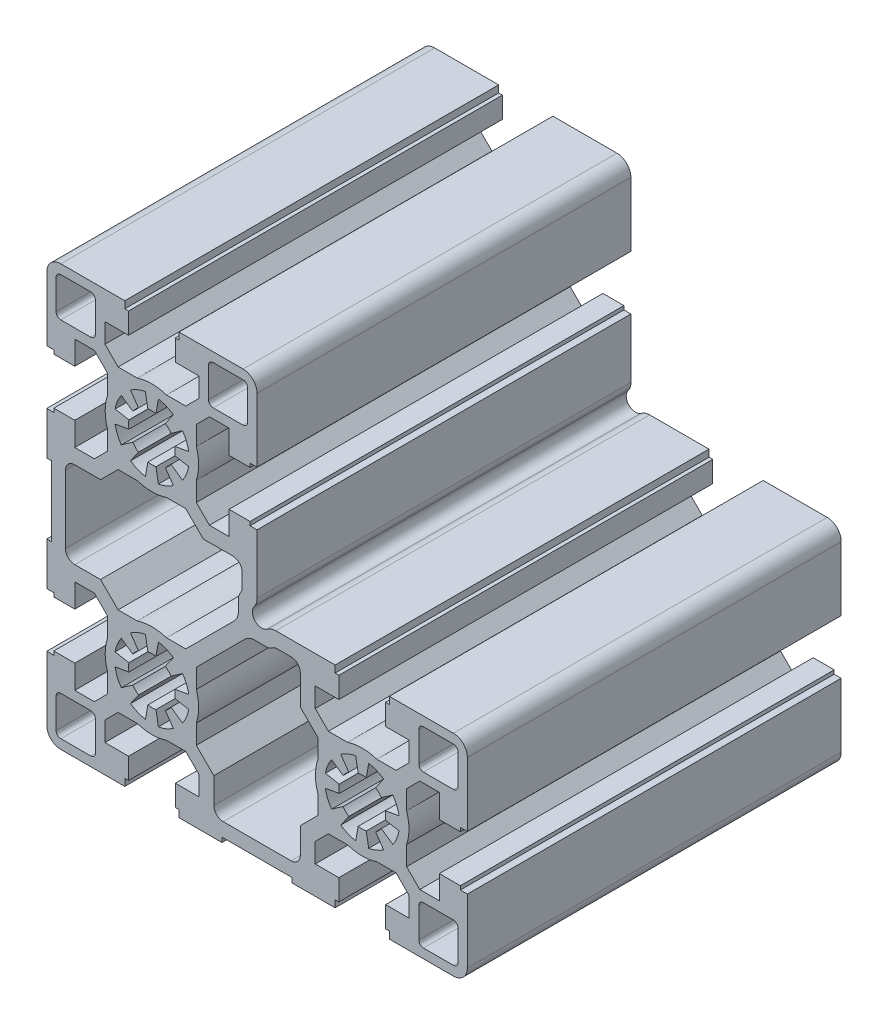
SolidWorks part; units mm, degrees
ref_plane "Front Plane" through (0, 0, 0) normal (0, 0, 1) x (1, 0, 0)
ref_plane "Top Plane" through (0, 0, 0) normal (0, 1, 0) x (1, 0, 0)
ref_plane "Right Plane" through (0, 0, 0) normal (1, 0, 0) x (0, 0, -1)
sketch "Sketch1" plane through (0, 0, 0) normal (0, 0, 1) x (1, 0, 0)
  line L0 (3.1734, -19.3822) -> (3.1734, -25.7822)
  line L1 (2.1734, -26.7822) -> (-4.2266, -26.7822)
  line L2 (-5.2266, -25.7822) -> (-5.2266, -19.3822)
  line L3 (-4.2266, -18.3822) -> (2.1734, -18.3822)
  line L4 (-81.8266, 61.2178) -> (-68.1266, 61.2178)
  line L5 (-56.5266, 61.2178) -> (-42.8266, 61.2178)
  line L6 (-36.9207, 12.4814) -> (-36.443, 12.7543)
  line L7 (-35.4507, 13.0178) -> (-32.5771, 13.0178)
  line L8 (-30.5771, 11.0178) -> (-30.5771, 4.7055)
  line L9 (-30.5771, 4.7055) -> (-26.8266, 0.9551)
  line L10 (-26.8266, 0.9551) -> (-26.8266, -3.1597)
  line L11 (-26.8266, -9.4047) -> (-26.8266, -13.5194)
  line L12 (-26.8266, -13.5194) -> (-30.5771, -17.2698)
  line L13 (-30.5771, -17.2698) -> (-30.5771, -22.7822)
  line L14 (-32.5771, -24.7822) -> (-47.0766, -24.7822)
  line L15 (-49.0766, -22.7822) -> (-49.0766, -17.2694)
  line L16 (-49.0766, -17.2694) -> (-52.8266, -13.5194)
  line L17 (-52.8266, -13.5194) -> (-52.8266, -9.4047)
  line L18 (-52.8266, -3.1597) -> (-52.8266, 0.9551)
  line L19 (-52.8266, 0.9551) -> (-42.4426, 11.3392)
  line L20 (-40.3212, 12.2178) -> (-37.9129, 12.2178)
  line L21 (-18.7158, 1.5963) -> (-18.1949, -1.3581)
  line L22 (-16.4584, -1.3581) -> (-15.9374, 1.5963)
  line L23 (-12.738, 0.2711) -> (-14.4587, -2.1864)
  line L24 (-13.2309, -3.4143) -> (-10.7734, -1.6935)
  line L25 (-9.4482, -4.893) -> (-12.4026, -5.4139)
  line L26 (-12.4026, -7.1504) -> (-9.4482, -7.6713)
  line L27 (-10.7734, -10.8708) -> (-13.2309, -9.15)
  line L28 (-14.4587, -10.3779) -> (-12.738, -12.8354)
  line L29 (-15.9374, -14.1606) -> (-16.4584, -11.2062)
  line L30 (-18.1949, -11.2062) -> (-18.7158, -14.1606)
  line L31 (-21.9152, -12.8354) -> (-20.1945, -10.3779)
  line L32 (-21.4224, -9.15) -> (-23.8798, -10.8708)
  line L33 (-25.2051, -7.6713) -> (-22.2507, -7.1504)
  line L34 (-22.2507, -5.4139) -> (-25.2051, -4.893)
  line L35 (-23.8798, -1.6935) -> (-21.4224, -3.4143)
  line L36 (-20.1945, -2.1864) -> (-21.9152, 0.2711)
  line L37 (-39.8266, 32.9178) -> (-39.8266, 20.2211)
  line L38 (-41.3266, 32.9178) -> (-39.8266, 32.9178)
  line L39 (-41.3266, 33.7178) -> (-41.3266, 32.9178)
  line L40 (-45.8266, 33.7178) -> (-41.3266, 33.7178)
  line L41 (-45.8266, 28.6678) -> (-45.8266, 33.7178)
  line L42 (-50.0139, 28.6678) -> (-45.8266, 28.6678)
  line L43 (-52.8266, 31.4806) -> (-50.0139, 28.6678)
  line L44 (-52.8266, 35.5953) -> (-52.8266, 31.4806)
  line L45 (-52.8266, 45.9551) -> (-52.8266, 41.8403)
  line L46 (-50.0139, 48.7678) -> (-52.8266, 45.9551)
  line L47 (-45.8266, 48.7678) -> (-50.0139, 48.7678)
  line L48 (-45.8266, 43.7178) -> (-45.8266, 48.7678)
  line L49 (-41.3266, 43.7178) -> (-45.8266, 43.7178)
  line L50 (-41.3266, 44.5178) -> (-41.3266, 43.7178)
  line L51 (-39.8266, 44.5178) -> (-41.3266, 44.5178)
  line L52 (-39.8266, 58.2178) -> (-39.8266, 44.5178)
  line L53 (-57.3266, 59.7178) -> (-56.5266, 59.7178)
  line L54 (-57.3266, 55.2178) -> (-57.3266, 59.7178)
  line L55 (-52.2766, 55.2178) -> (-57.3266, 55.2178)
  line L56 (-52.2766, 51.0306) -> (-52.2766, 55.2178)
  line L57 (-55.0894, 48.2178) -> (-52.2766, 51.0306)
  line L58 (-59.2041, 48.2178) -> (-55.0894, 48.2178)
  line L59 (-69.5639, 48.2178) -> (-65.4491, 48.2178)
  line L60 (-72.3766, 51.0306) -> (-69.5639, 48.2178)
  line L61 (-72.3766, 55.2178) -> (-72.3766, 51.0306)
  line L62 (-67.3266, 55.2178) -> (-72.3766, 55.2178)
  line L63 (-67.3266, 59.7178) -> (-67.3266, 55.2178)
  line L64 (-68.1266, 59.7178) -> (-67.3266, 59.7178)
  line L65 (-84.8266, 44.5178) -> (-84.8266, 58.2178)
  line L66 (-83.3266, 44.5178) -> (-84.8266, 44.5178)
  line L67 (-83.3266, 43.7178) -> (-83.3266, 44.5178)
  line L68 (-78.8266, 43.7178) -> (-83.3266, 43.7178)
  line L69 (-78.8266, 48.7678) -> (-78.8266, 43.7178)
  line L70 (-74.6394, 48.7678) -> (-78.8266, 48.7678)
  line L71 (-71.8266, 45.9551) -> (-74.6394, 48.7678)
  line L72 (-71.8266, 41.8403) -> (-71.8266, 45.9551)
  line L73 (-71.8266, 31.4806) -> (-71.8266, 35.5953)
  line L74 (-74.6394, 28.6678) -> (-71.8266, 31.4806)
  line L75 (-78.8266, 28.6678) -> (-74.6394, 28.6678)
  line L76 (-78.8266, 33.7178) -> (-78.8266, 28.6678)
  line L77 (-83.3266, 33.7178) -> (-78.8266, 33.7178)
  line L78 (-83.3266, 32.9178) -> (-83.3266, 33.7178)
  line L79 (-84.8266, 32.9178) -> (-83.3266, 32.9178)
  line L80 (-84.8266, 23.7178) -> (-84.8266, 32.9178)
  line L81 (-83.8266, 23.7178) -> (-84.8266, 23.7178)
  line L82 (-83.8266, 8.7178) -> (-83.8266, 23.7178)
  line L83 (-84.8266, 8.7178) -> (-83.8266, 8.7178)
  line L84 (-84.8266, -0.4822) -> (-84.8266, 8.7178)
  line L85 (-83.3266, -0.4822) -> (-84.8266, -0.4822)
  line L86 (-83.3266, -1.2822) -> (-83.3266, -0.4822)
  line L87 (-78.8266, -1.2822) -> (-83.3266, -1.2822)
  line L88 (-78.8266, 3.7678) -> (-78.8266, -1.2822)
  line L89 (-74.6394, 3.7678) -> (-78.8266, 3.7678)
  line L90 (-71.8266, 0.9551) -> (-74.6394, 3.7678)
  line L91 (-71.8266, -3.1597) -> (-71.8266, 0.9551)
  line L92 (-71.8266, -13.5194) -> (-71.8266, -9.4047)
  line L93 (-74.6394, -16.3322) -> (-71.8266, -13.5194)
  line L94 (-78.8266, -16.3322) -> (-74.6394, -16.3322)
  line L95 (-78.8266, -11.2822) -> (-78.8266, -16.3322)
  line L96 (-83.3266, -11.2822) -> (-78.8266, -11.2822)
  line L97 (-83.3266, -12.0822) -> (-83.3266, -11.2822)
  line L98 (-84.8266, -12.0822) -> (-83.3266, -12.0822)
  line L99 (-84.8266, -25.7822) -> (-84.8266, -12.0822)
  line L100 (-68.1266, -28.7822) -> (-81.8266, -28.7822)
  line L101 (-68.1266, -27.2822) -> (-68.1266, -28.7822)
  line L102 (-67.3266, -27.2822) -> (-68.1266, -27.2822)
  line L103 (-67.3266, -22.7822) -> (-67.3266, -27.2822)
  line L104 (-72.3766, -22.7822) -> (-67.3266, -22.7822)
  line L105 (-72.3766, -18.5949) -> (-72.3766, -22.7822)
  line L106 (-69.5639, -15.7822) -> (-72.3766, -18.5949)
  line L107 (-65.4491, -15.7822) -> (-69.5639, -15.7822)
  line L108 (-55.0894, -15.7822) -> (-59.2041, -15.7822)
  line L109 (-52.2766, -18.5949) -> (-55.0894, -15.7822)
  line L110 (-52.2766, -22.7822) -> (-52.2766, -18.5949)
  line L111 (-57.3266, -22.7822) -> (-52.2766, -22.7822)
  line L112 (-57.3266, -27.2822) -> (-57.3266, -22.7822)
  line L113 (-56.5266, -27.2822) -> (-57.3266, -27.2822)
  line L114 (-56.5266, -28.7822) -> (-56.5266, -27.2822)
  line L115 (-47.3266, -28.7822) -> (-56.5266, -28.7822)
  line L116 (-47.3266, -27.7822) -> (-47.3266, -28.7822)
  line L117 (-32.3266, -27.7822) -> (-47.3266, -27.7822)
  line L118 (-32.3266, -28.7822) -> (-32.3266, -27.7822)
  line L119 (-23.1266, -28.7822) -> (-32.3266, -28.7822)
  line L120 (-23.1266, -27.2822) -> (-23.1266, -28.7822)
  line L121 (-22.3266, -27.2822) -> (-23.1266, -27.2822)
  line L122 (-22.3266, -22.7822) -> (-22.3266, -27.2822)
  line L123 (-27.3766, -22.7822) -> (-22.3266, -22.7822)
  line L124 (-27.3766, -18.5949) -> (-27.3766, -22.7822)
  line L125 (-24.5639, -15.7822) -> (-27.3766, -18.5949)
  line L126 (-20.4491, -15.7822) -> (-24.5639, -15.7822)
  line L127 (-10.0894, -15.7822) -> (-14.2041, -15.7822)
  line L128 (-7.2766, -18.5949) -> (-10.0894, -15.7822)
  line L129 (-7.2766, -22.7822) -> (-7.2766, -18.5949)
  line L130 (-12.3266, -22.7822) -> (-7.2766, -22.7822)
  line L131 (-12.3266, -27.2822) -> (-12.3266, -22.7822)
  line L132 (-11.5266, -27.2822) -> (-12.3266, -27.2822)
  line L133 (-11.5266, -28.7822) -> (-11.5266, -27.2822)
  line L134 (2.1734, -28.7822) -> (-11.5266, -28.7822)
  line L135 (5.1734, -12.0822) -> (5.1734, -25.7822)
  line L136 (3.6734, -12.0822) -> (5.1734, -12.0822)
  line L137 (3.6734, -11.2822) -> (3.6734, -12.0822)
  line L138 (-0.8266, -11.2822) -> (3.6734, -11.2822)
  line L139 (-0.8266, -16.3322) -> (-0.8266, -11.2822)
  line L140 (-5.0139, -16.3322) -> (-0.8266, -16.3322)
  line L141 (-7.8266, -13.5194) -> (-5.0139, -16.3322)
  line L142 (-7.8266, -9.4047) -> (-7.8266, -13.5194)
  line L143 (-7.8266, 0.9551) -> (-7.8266, -3.1597)
  line L144 (-5.0139, 3.7678) -> (-7.8266, 0.9551)
  line L145 (-0.8266, 3.7678) -> (-5.0139, 3.7678)
  line L146 (-0.8266, -1.2822) -> (-0.8266, 3.7678)
  line L147 (3.6734, -1.2822) -> (-0.8266, -1.2822)
  line L148 (3.6734, -0.4822) -> (3.6734, -1.2822)
  line L149 (5.1734, -0.4822) -> (3.6734, -0.4822)
  line L150 (5.1734, 13.2178) -> (5.1734, -0.4822)
  line L151 (-11.5266, 16.2178) -> (2.1734, 16.2178)
  line L152 (-11.5266, 14.7178) -> (-11.5266, 16.2178)
  line L153 (-12.3266, 14.7178) -> (-11.5266, 14.7178)
  line L154 (-12.3266, 10.2178) -> (-12.3266, 14.7178)
  line L155 (-7.2766, 10.2178) -> (-12.3266, 10.2178)
  line L156 (-7.2766, 6.0306) -> (-7.2766, 10.2178)
  line L157 (-10.0894, 3.2178) -> (-7.2766, 6.0306)
  line L158 (-14.2041, 3.2178) -> (-10.0894, 3.2178)
  line L159 (-24.5639, 3.2178) -> (-20.4491, 3.2178)
  line L160 (-27.3766, 6.0306) -> (-24.5639, 3.2178)
  line L161 (-27.3766, 10.2178) -> (-27.3766, 6.0306)
  line L162 (-22.3266, 10.2178) -> (-27.3766, 10.2178)
  line L163 (-22.3266, 14.7178) -> (-22.3266, 10.2178)
  line L164 (-23.1266, 14.7178) -> (-22.3266, 14.7178)
  line L165 (-23.1266, 16.2178) -> (-23.1266, 14.7178)
  line L166 (-35.8233, 16.2178) -> (-23.1266, 16.2178)
  line L167 (-4.2266, 14.2178) -> (2.1734, 14.2178)
  line L168 (3.1734, 13.2178) -> (3.1734, 6.8178)
  line L169 (2.1734, 5.8178) -> (-4.2266, 5.8178)
  line L170 (-5.2266, 6.8178) -> (-5.2266, 13.2178)
  line L171 (-42.8266, 50.8178) -> (-49.2266, 50.8178)
  line L172 (-50.2266, 51.8178) -> (-50.2266, 58.2178)
  line L173 (-49.2266, 59.2178) -> (-42.8266, 59.2178)
  line L174 (-41.8266, 58.2178) -> (-41.8266, 51.8178)
  line L175 (-63.7158, 46.5963) -> (-63.1949, 43.6419)
  line L176 (-61.4584, 43.6419) -> (-60.9374, 46.5963)
  line L177 (-57.738, 45.2711) -> (-59.4587, 42.8136)
  line L178 (-58.2309, 41.5857) -> (-55.7734, 43.3065)
  line L179 (-54.4482, 40.107) -> (-57.4026, 39.5861)
  line L180 (-57.4026, 37.8496) -> (-54.4482, 37.3287)
  line L181 (-55.7734, 34.1292) -> (-58.2309, 35.85)
  line L182 (-59.4587, 34.6221) -> (-57.738, 32.1646)
  line L183 (-60.9374, 30.8394) -> (-61.4584, 33.7938)
  line L184 (-63.1949, 33.7938) -> (-63.7158, 30.8394)
  line L185 (-66.9152, 32.1646) -> (-65.1945, 34.6221)
  line L186 (-66.4224, 35.85) -> (-68.8798, 34.1292)
  line L187 (-70.2051, 37.3287) -> (-67.2507, 37.8496)
  line L188 (-67.2507, 39.5861) -> (-70.2051, 40.107)
  line L189 (-68.8798, 43.3065) -> (-66.4224, 41.5857)
  line L190 (-65.1945, 42.8136) -> (-66.9152, 45.2711)
  line L191 (-44.7053, 13.6019) -> (-55.0894, 3.2178)
  line L192 (-55.0894, 3.2178) -> (-59.2041, 3.2178)
  line L193 (-65.4491, 3.2178) -> (-69.5639, 3.2178)
  line L194 (-69.5639, 3.2178) -> (-73.3139, 6.9678)
  line L195 (-73.3139, 6.9678) -> (-78.8266, 6.9678)
  line L196 (-80.8266, 8.9678) -> (-80.8266, 23.4674)
  line L197 (-78.8266, 25.4674) -> (-73.3143, 25.4674)
  line L198 (-73.3143, 25.4674) -> (-69.5639, 29.2178)
  line L199 (-69.5639, 29.2178) -> (-65.4491, 29.2178)
  line L200 (-59.2041, 29.2178) -> (-55.0894, 29.2178)
  line L201 (-55.0894, 29.2178) -> (-51.3389, 25.4674)
  line L202 (-51.3389, 25.4674) -> (-45.0266, 25.4674)
  line L203 (-43.0266, 23.4674) -> (-43.0266, 20.5938)
  line L204 (-43.2901, 19.6015) -> (-43.5631, 19.1238)
  line L205 (-43.8266, 18.1315) -> (-43.8266, 15.7232)
  line L206 (-63.7158, 1.5963) -> (-63.1949, -1.3581)
  line L207 (-61.4584, -1.3581) -> (-60.9374, 1.5963)
  line L208 (-57.738, 0.2711) -> (-59.4587, -2.1864)
  line L209 (-58.2309, -3.4143) -> (-55.7734, -1.6935)
  line L210 (-54.4482, -4.893) -> (-57.4026, -5.4139)
  line L211 (-57.4026, -7.1504) -> (-54.4482, -7.6713)
  line L212 (-55.7734, -10.8708) -> (-58.2309, -9.15)
  line L213 (-59.4587, -10.3779) -> (-57.738, -12.8354)
  line L214 (-60.9374, -14.1606) -> (-61.4584, -11.2062)
  line L215 (-63.1949, -11.2062) -> (-63.7158, -14.1606)
  line L216 (-66.9152, -12.8354) -> (-65.1945, -10.3779)
  line L217 (-66.4224, -9.15) -> (-68.8798, -10.8708)
  line L218 (-70.2051, -7.6713) -> (-67.2507, -7.1504)
  line L219 (-67.2507, -5.4139) -> (-70.2051, -4.893)
  line L220 (-68.8798, -1.6935) -> (-66.4224, -3.4143)
  line L221 (-65.1945, -2.1864) -> (-66.9152, 0.2711)
  line L222 (-82.8266, 51.8178) -> (-82.8266, 58.2178)
  line L223 (-81.8266, 59.2178) -> (-75.4266, 59.2178)
  line L224 (-74.4266, 58.2178) -> (-74.4266, 51.8178)
  line L225 (-75.4266, 50.8178) -> (-81.8266, 50.8178)
  line L226 (-75.4266, -26.7822) -> (-81.8266, -26.7822)
  line L227 (-82.8266, -25.7822) -> (-82.8266, -19.3822)
  line L228 (-81.8266, -18.3822) -> (-75.4266, -18.3822)
  line L229 (-74.4266, -19.3822) -> (-74.4266, -25.7822)
  line L230 (-68.1266, 61.2178) -> (-68.1266, 59.7178)
  line L231 (-56.5266, 59.7178) -> (-56.5266, 61.2178)
  arc A0 (2.1734, -18.3822) -> (3.1734, -19.3822) centre (2.1734, -19.3822) cw
  arc A1 (3.1734, -25.7822) -> (2.1734, -26.7822) centre (2.1734, -25.7822) cw
  arc A2 (-4.2266, -26.7822) -> (-5.2266, -25.7822) centre (-4.2266, -25.7822) cw
  arc A3 (-5.2266, -19.3822) -> (-4.2266, -18.3822) centre (-4.2266, -19.3822) cw
  arc A4 (2.1734, 14.2178) -> (3.1734, 13.2178) centre (2.1734, 13.2178) cw
  arc A5 (3.1734, 6.8178) -> (2.1734, 5.8178) centre (2.1734, 6.8178) cw
  arc A6 (-4.2266, 5.8178) -> (-5.2266, 6.8178) centre (-4.2266, 6.8178) cw
  arc A7 (-5.2266, 13.2178) -> (-4.2266, 14.2178) centre (-4.2266, 13.2178) cw
  arc A8 (-36.9207, 12.4814) -> (-37.9129, 12.2178) centre (-37.9129, 14.2178) cw
  arc A9 (-36.443, 12.7543) -> (-35.4507, 13.0178) centre (-35.4507, 11.0178) cw
  arc A10 (-32.5771, 13.0178) -> (-30.5771, 11.0178) centre (-32.5771, 11.0178) cw
  arc A11 (-26.8266, -9.4047) -> (-26.8266, -3.1597) centre (-17.3266, -6.2822) cw
  arc A12 (-30.5771, -22.7822) -> (-32.5771, -24.7822) centre (-32.5771, -22.7822) cw
  arc A13 (-47.0766, -24.7822) -> (-49.0766, -22.7822) centre (-47.0766, -22.7822) cw
  arc A14 (-52.8266, -3.1597) -> (-52.8266, -9.4047) centre (-62.3266, -6.2822) cw
  arc A15 (-42.4426, 11.3392) -> (-40.3212, 12.2178) centre (-40.3212, 9.2178) cw
  arc A16 (-21.9152, 0.2711) -> (-18.7158, 1.5963) centre (-17.3266, -6.2822) cw
  arc A17 (-18.1949, -1.3581) -> (-16.4584, -1.3581) centre (-17.3266, -6.2822) cw
  arc A18 (-15.9374, 1.5963) -> (-12.738, 0.2711) centre (-17.3266, -6.2822) cw
  arc A19 (-14.4587, -2.1864) -> (-13.2309, -3.4143) centre (-17.3266, -6.2822) cw
  arc A20 (-10.7734, -1.6935) -> (-9.4482, -4.893) centre (-17.3266, -6.2822) cw
  arc A21 (-12.4026, -5.4139) -> (-12.4026, -7.1504) centre (-17.3266, -6.2822) cw
  arc A22 (-9.4482, -7.6713) -> (-10.7734, -10.8708) centre (-17.3266, -6.2822) cw
  arc A23 (-13.2309, -9.15) -> (-14.4587, -10.3779) centre (-17.3266, -6.2822) cw
  arc A24 (-12.738, -12.8354) -> (-15.9374, -14.1606) centre (-17.3266, -6.2822) cw
  arc A25 (-16.4584, -11.2062) -> (-18.1949, -11.2062) centre (-17.3266, -6.2822) cw
  arc A26 (-18.7158, -14.1606) -> (-21.9152, -12.8354) centre (-17.3266, -6.2822) cw
  arc A27 (-20.1945, -10.3779) -> (-21.4224, -9.15) centre (-17.3266, -6.2822) cw
  arc A28 (-23.8798, -10.8708) -> (-25.2051, -7.6713) centre (-17.3266, -6.2822) cw
  arc A29 (-22.2507, -7.1504) -> (-22.2507, -5.4139) centre (-17.3266, -6.2822) cw
  arc A30 (-25.2051, -4.893) -> (-23.8798, -1.6935) centre (-17.3266, -6.2822) cw
  arc A31 (-21.4224, -3.4143) -> (-20.1945, -2.1864) centre (-17.3266, -6.2822) cw
  arc A32 (-49.2266, 50.8178) -> (-50.2266, 51.8178) centre (-49.2266, 51.8178) cw
  arc A33 (-50.2266, 58.2178) -> (-49.2266, 59.2178) centre (-49.2266, 58.2178) cw
  arc A34 (-42.8266, 59.2178) -> (-41.8266, 58.2178) centre (-42.8266, 58.2178) cw
  arc A35 (-41.8266, 51.8178) -> (-42.8266, 50.8178) centre (-42.8266, 51.8178) cw
  arc A36 (-66.9152, 45.2711) -> (-63.7158, 46.5963) centre (-62.3266, 38.7178) cw
  arc A37 (-63.1949, 43.6419) -> (-61.4584, 43.6419) centre (-62.3266, 38.7178) cw
  arc A38 (-60.9374, 46.5963) -> (-57.738, 45.2711) centre (-62.3266, 38.7178) cw
  arc A39 (-59.4587, 42.8136) -> (-58.2309, 41.5857) centre (-62.3266, 38.7178) cw
  arc A40 (-55.7734, 43.3065) -> (-54.4482, 40.107) centre (-62.3266, 38.7178) cw
  arc A41 (-57.4026, 39.5861) -> (-57.4026, 37.8496) centre (-62.3266, 38.7178) cw
  arc A42 (-54.4482, 37.3287) -> (-55.7734, 34.1292) centre (-62.3266, 38.7178) cw
  arc A43 (-58.2309, 35.85) -> (-59.4587, 34.6221) centre (-62.3266, 38.7178) cw
  arc A44 (-57.738, 32.1646) -> (-60.9374, 30.8394) centre (-62.3266, 38.7178) cw
  arc A45 (-61.4584, 33.7938) -> (-63.1949, 33.7938) centre (-62.3266, 38.7178) cw
  arc A46 (-63.7158, 30.8394) -> (-66.9152, 32.1646) centre (-62.3266, 38.7178) cw
  arc A47 (-65.1945, 34.6221) -> (-66.4224, 35.85) centre (-62.3266, 38.7178) cw
  arc A48 (-68.8798, 34.1292) -> (-70.2051, 37.3287) centre (-62.3266, 38.7178) cw
  arc A49 (-67.2507, 37.8496) -> (-67.2507, 39.5861) centre (-62.3266, 38.7178) cw
  arc A50 (-70.2051, 40.107) -> (-68.8798, 43.3065) centre (-62.3266, 38.7178) cw
  arc A51 (-66.4224, 41.5857) -> (-65.1945, 42.8136) centre (-62.3266, 38.7178) cw
  arc A52 (-81.8266, 50.8178) -> (-82.8266, 51.8178) centre (-81.8266, 51.8178) cw
  arc A53 (-82.8266, 58.2178) -> (-81.8266, 59.2178) centre (-81.8266, 58.2178) cw
  arc A54 (-75.4266, 59.2178) -> (-74.4266, 58.2178) centre (-75.4266, 58.2178) cw
  arc A55 (-74.4266, 51.8178) -> (-75.4266, 50.8178) centre (-75.4266, 51.8178) cw
  arc A56 (-43.8266, 15.7232) -> (-44.7053, 13.6019) centre (-46.8266, 15.7232) cw
  arc A57 (-65.4491, 3.2178) -> (-59.2041, 3.2178) centre (-62.3266, -6.2822) cw
  arc A58 (-78.8266, 6.9678) -> (-80.8266, 8.9678) centre (-78.8266, 8.9678) cw
  arc A59 (-80.8266, 23.4674) -> (-78.8266, 25.4674) centre (-78.8266, 23.4674) cw
  arc A60 (-59.2041, 29.2178) -> (-65.4491, 29.2178) centre (-62.3266, 38.7178) cw
  arc A61 (-45.0266, 25.4674) -> (-43.0266, 23.4674) centre (-45.0266, 23.4674) cw
  arc A62 (-43.0266, 20.5938) -> (-43.2901, 19.6015) centre (-45.0266, 20.5938) cw
  arc A63 (-43.8266, 18.1315) -> (-43.5631, 19.1238) centre (-41.8266, 18.1315) cw
  arc A64 (-66.9152, 0.2711) -> (-63.7158, 1.5963) centre (-62.3266, -6.2822) cw
  arc A65 (-63.1949, -1.3581) -> (-61.4584, -1.3581) centre (-62.3266, -6.2822) cw
  arc A66 (-60.9374, 1.5963) -> (-57.738, 0.2711) centre (-62.3266, -6.2822) cw
  arc A67 (-59.4587, -2.1864) -> (-58.2309, -3.4143) centre (-62.3266, -6.2822) cw
  arc A68 (-55.7734, -1.6935) -> (-54.4482, -4.893) centre (-62.3266, -6.2822) cw
  arc A69 (-57.4026, -5.4139) -> (-57.4026, -7.1504) centre (-62.3266, -6.2822) cw
  arc A70 (-54.4482, -7.6713) -> (-55.7734, -10.8708) centre (-62.3266, -6.2822) cw
  arc A71 (-58.2309, -9.15) -> (-59.4587, -10.3779) centre (-62.3266, -6.2822) cw
  arc A72 (-57.738, -12.8354) -> (-60.9374, -14.1606) centre (-62.3266, -6.2822) cw
  arc A73 (-61.4584, -11.2062) -> (-63.1949, -11.2062) centre (-62.3266, -6.2822) cw
  arc A74 (-63.7158, -14.1606) -> (-66.9152, -12.8354) centre (-62.3266, -6.2822) cw
  arc A75 (-65.1945, -10.3779) -> (-66.4224, -9.15) centre (-62.3266, -6.2822) cw
  arc A76 (-68.8798, -10.8708) -> (-70.2051, -7.6713) centre (-62.3266, -6.2822) cw
  arc A77 (-67.2507, -7.1504) -> (-67.2507, -5.4139) centre (-62.3266, -6.2822) cw
  arc A78 (-70.2051, -4.893) -> (-68.8798, -1.6935) centre (-62.3266, -6.2822) cw
  arc A79 (-66.4224, -3.4143) -> (-65.1945, -2.1864) centre (-62.3266, -6.2822) cw
  arc A80 (-37.6313, 15.6118) -> (-40.4327, 18.4131) centre (-38.8367, 17.2078) cw
  arc A81 (-39.8266, 20.2211) -> (-40.4327, 18.4131) centre (-42.8266, 20.2211) cw
  arc A82 (-52.8266, 41.8403) -> (-52.8266, 35.5953) centre (-62.3266, 38.7178) cw
  arc A83 (-42.8266, 61.2178) -> (-39.8266, 58.2178) centre (-42.8266, 58.2178) cw
  arc A84 (-65.4491, 48.2178) -> (-59.2041, 48.2178) centre (-62.3266, 38.7178) cw
  arc A85 (-84.8266, 58.2178) -> (-81.8266, 61.2178) centre (-81.8266, 58.2178) cw
  arc A86 (-71.8266, 35.5953) -> (-71.8266, 41.8403) centre (-62.3266, 38.7178) cw
  arc A87 (-71.8266, -9.4047) -> (-71.8266, -3.1597) centre (-62.3266, -6.2822) cw
  arc A88 (-81.8266, -28.7822) -> (-84.8266, -25.7822) centre (-81.8266, -25.7822) cw
  arc A89 (-59.2041, -15.7822) -> (-65.4491, -15.7822) centre (-62.3266, -6.2822) cw
  arc A90 (-14.2041, -15.7822) -> (-20.4491, -15.7822) centre (-17.3266, -6.2822) cw
  arc A91 (5.1734, -25.7822) -> (2.1734, -28.7822) centre (2.1734, -25.7822) cw
  arc A92 (-7.8266, -3.1597) -> (-7.8266, -9.4047) centre (-17.3266, -6.2822) cw
  arc A93 (2.1734, 16.2178) -> (5.1734, 13.2178) centre (2.1734, 13.2178) cw
  arc A94 (-20.4491, 3.2178) -> (-14.2041, 3.2178) centre (-17.3266, -6.2822) cw
  arc A95 (-37.6313, 15.6118) -> (-35.8233, 16.2178) centre (-35.8233, 13.2178) cw
  arc A96 (-74.4266, -25.7822) -> (-75.4266, -26.7822) centre (-75.4266, -25.7822) cw
  arc A97 (-81.8266, -26.7822) -> (-82.8266, -25.7822) centre (-81.8266, -25.7822) cw
  arc A98 (-82.8266, -19.3822) -> (-81.8266, -18.3822) centre (-81.8266, -19.3822) cw
  arc A99 (-75.4266, -18.3822) -> (-74.4266, -19.3822) centre (-75.4266, -19.3822) cw
extrude "Extrude1" add sketch "Sketch1" against normal blind 80
